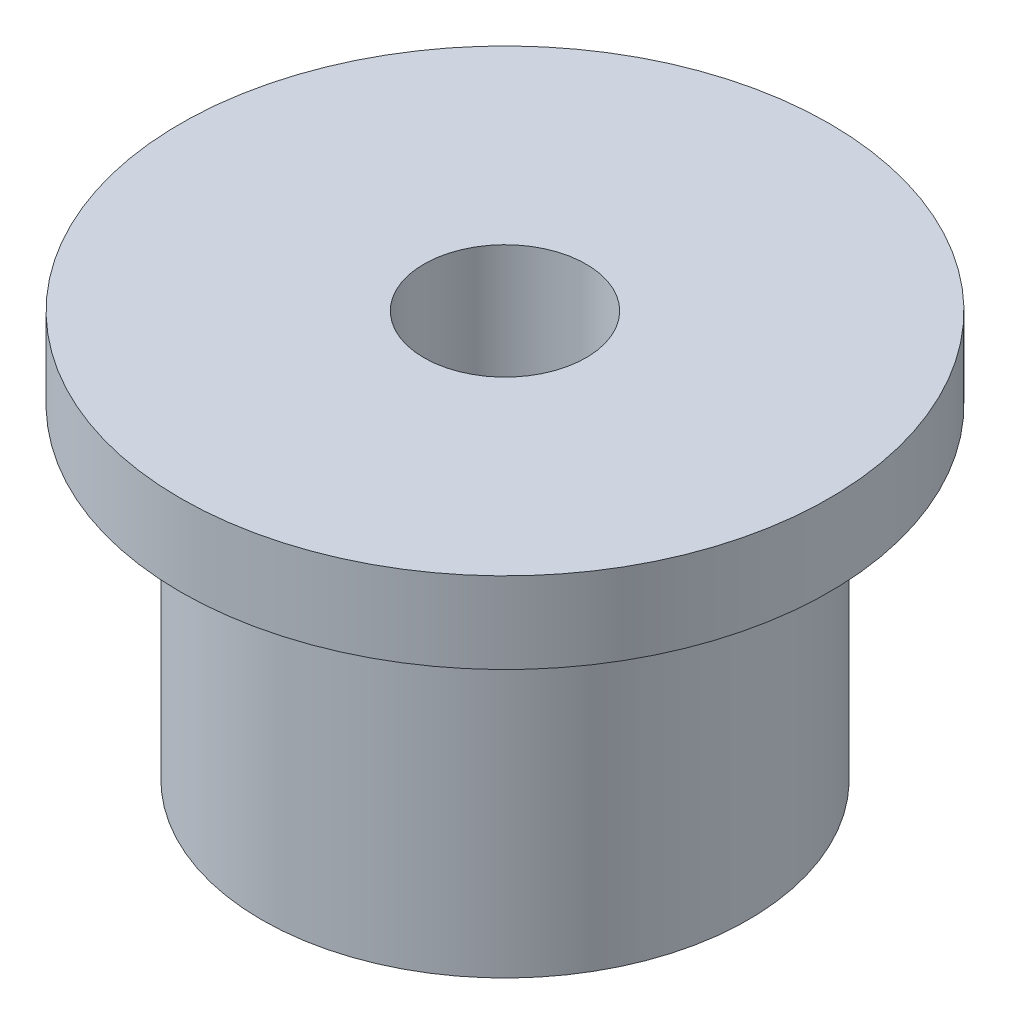
SolidWorks part; units mm, degrees
ref_plane "Front Plane" through (0, 0, 0) normal (0, 0, 1) x (1, 0, 0)
ref_plane "Top Plane" through (0, 0, 0) normal (0, 1, 0) x (1, 0, 0)
ref_plane "Right Plane" through (0, 0, 0) normal (1, 0, 0) x (0, 0, -1)
sketch "Sketch1" plane through (0, 0, 0) normal (0, 0, 1) x (1, 0, 0)
  line L0 (0, 62.5) -> (0, -62.5) construction
  line L1 (25, 62.5) -> (100, 62.5)
  line L2 (100, 62.5) -> (100, 37.5)
  line L3 (25, -62.5) -> (75, -62.5)
  line L4 (75, -62.5) -> (75, 37.5)
  line L5 (75, 37.5) -> (100, 37.5)
  line L6 (25, 62.5) -> (25, -62.5)
  point P4 (0, 0)
  dimension "D1" = 25
revolve "Revolve1" add sketch "Sketch1" angle 360 about L0
